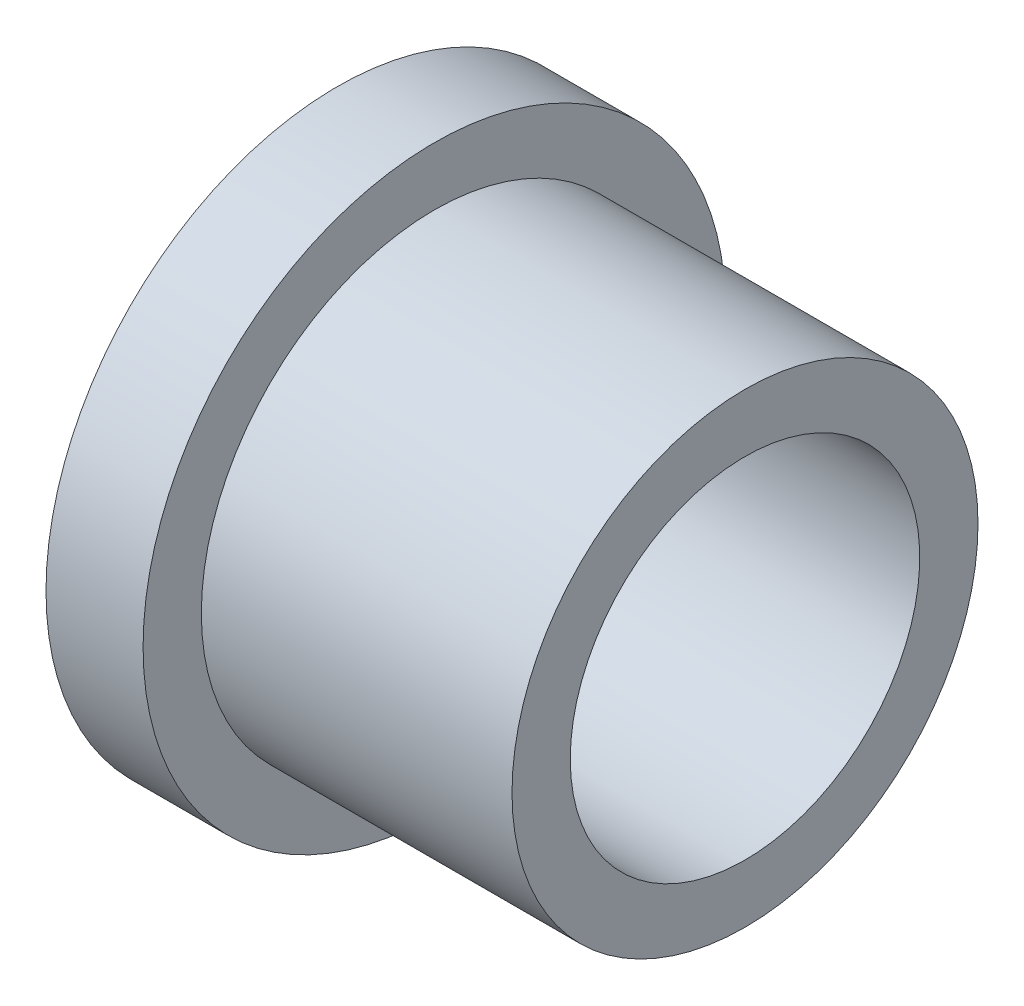
SolidWorks part; units mm, degrees
ref_plane "Front Plane" through (0, 0, 0) normal (0, 0, 1) x (1, 0, 0)
ref_plane "Top Plane" through (0, 0, 0) normal (0, 1, 0) x (1, 0, 0)
ref_plane "Right Plane" through (0, 0, 0) normal (1, 0, 0) x (0, 0, -1)
sketch "Sketch1" plane through (0, 0, 0) normal (0, 0, 1) x (1, 0, 0)
  line L0 (0, 9) -> (21, 9)
  line L1 (21, 9) -> (21, 12)
  line L2 (21, 12) -> (5, 12)
  line L3 (5, 12) -> (5, 15)
  line L4 (5, 15) -> (0, 15)
  line L5 (0, 15) -> (0, 9)
  line L6 (0, 0) -> (16.9186, 0) construction
  dimension "D1" = 30
  dimension "D2" = 3
  dimension "D3" = 16
  dimension "D4" = 21
  dimension "D5" = 24
revolve "Revolve1" add sketch "Sketch1" angle 360 about L6
